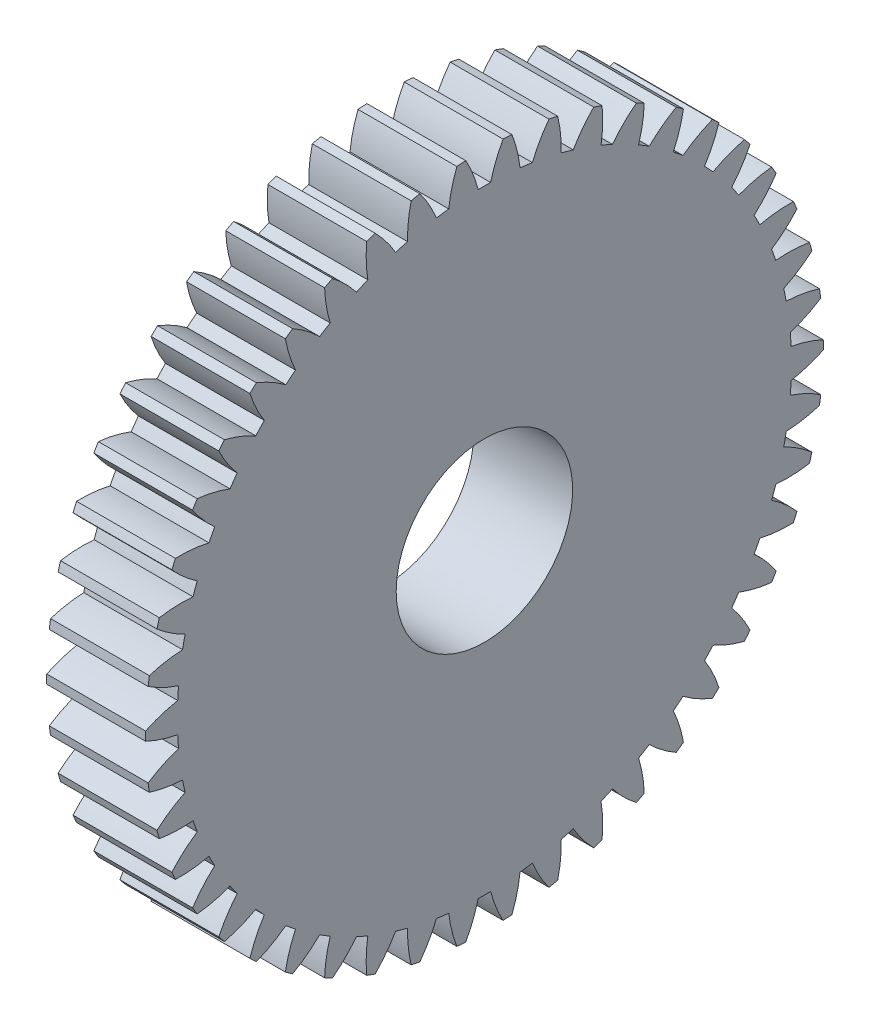
SolidWorks part; units mm, degrees
ref_plane "Plane1" through (0, 0, 0) normal (0, 0, 1) x (1, 0, 0)
ref_plane "Plane2" through (0, 0, 0) normal (0, 1, 0) x (1, 0, 0)
ref_plane "Plane3" through (0, 0, 0) normal (1, 0, 0) x (0, 0, -1)
sketch "HoldingSke" plane through (0, 0, 0) normal (0, 1, 0) x (1, 0, 0)
  line L0 (0, 0) -> (1.7366, -1.7983)
  line L1 (-15, 0) -> (100, 0) construction
  line L2 (0, 0) -> (-2.1039, 2.3779)
  line L3 (0, 0) -> (-11.863, 4.5341)
  line L4 (0, 0) -> (5.9991, 6.2122)
  line L5 (0, 0) -> (-46.8476, -17.4728)
  line L6 (0, 0) -> (-2.3211, -1.5661)
  line L7 (-2.1039, 2.3779) -> (8.6586, 51.2059)
  line L8 (-76.2, 54.61) -> (-75.3, 54.61)
  line L9 (-71.009, 38.7566) -> (-53.1078, 45.2721)
  line L10 (-76.2, 71.12) -> (104.1128, 71.12)
  line L11 (0, 0) -> (-2.8, 0)
  line L12 (-76.2, 101.6) -> (-76.185, 101.6)
  line L13 (24.9733, 27.94) -> (52.9518, 28.4284)
  line L14 (24.9733, 27.94) -> (24.9743, 27.94)
  line L15 (24.9733, 27.94) -> (100.4006, 29.5858)
  line L16 (-63.627, -0.4) -> (-12.827, -0.4)
  circle A0 centre (0, 0) radius 2.5
  circle A1 centre (0, 0) radius 8.699
  circle A2 centre (0, 0) radius 37.5
  circle A3 centre (0, 0) radius 2.5
  dimension "Hub_dia" = 75
  dimension "Overall_len" = 50
  dimension "OAL" = 50.0001
  dimension "Ap" = 20
  dimension "H" = 19.05
  dimension "Pitch_radius" = 180.3128
  dimension "Addendum_fac" = 1
  dimension "Dedendum_fac" = 1.25
  dimension "Clearance_fac" = 0.25
  dimension "Dedendum_add" = 0.001
sketch "BasProSke" plane through (0, 0, 0) normal (0, 1, 0) x (1, 0, 0)
  line L0 (-10, 0) -> (60, 0) construction
  line L1 (0, 0) -> (0, 9.6)
  line L2 (0, 0) -> (2.8, 0)
  line L3 (2.8, 0) -> (2.8, 9.6)
  line L4 (2.8, 9.6) -> (0, 9.6)
revolve "Base-Revolve" add sketch "BasProSke" angle 360 about L0
sketch "TooCutSke" plane through (0, 0, 0) normal (1, 0, 0) x (0, 0, -1)
  line L1 (0, 0) -> (0, 107) construction
  line L2 (0, 0) -> (-0.3403, 9.1937) construction
  line L3 (0, 0) -> (-1.255, 18.3481) construction
  line L4 (-0.3403, 9.1937) -> (-0.6275, 9.1741) construction
  arc A0 (0.1761, 8.6972) -> (-0.1761, 8.6972) centre (0, 0) ccw
  arc A1 (0.5433, 9.6101) -> (-0.5433, 9.6101) centre (0, 0) ccw
  circle A2 centre (0, 0) radius 9.2 construction
  circle A3 centre (0, 0) radius 8.6452 construction
  arc A4 (-0.1761, 8.6972) -> (-0.5433, 9.6101) centre (-3.7432, 7.7928) ccw
  arc A5 (0.5433, 9.6101) -> (0.1761, 8.6972) centre (3.7432, 7.7928) ccw
extrude "ToothCut" cut sketch "TooCutSke" along normal through all
fillet "Breaks" [suppressed] radius 0.008
fillet "RootFillets" [suppressed] radius 0.101
pattern_circular "TeethCuts" count 46 every 7.826 about axis through (-10, 0, 0) along (1, 0, 0) of "ToothCut", "RootFillets", "Breaks"
sketch "HubNeaOneSke" plane through (0, 0, 0) normal (-1, 0, 0) x (0, 0, 1)
  circle A0 centre (0, 0) radius 8.699
extrude "HubNearOne" [suppressed] add sketch "HubNeaOneSke" along normal blind 47.2001
sketch "HubNeaBotSke" plane through (0, 0, 0) normal (-1, 0, 0) x (0, 0, 1)
  circle A0 centre (0, 0) radius 8.699
extrude "HubNearBoth" [suppressed] add sketch "HubNeaBotSke" along normal blind 23.6
ref_plane "FarPln" through (2.8, 0, 0) normal (1, 0, 0) x (0, 0, -1)
sketch "HubFarSke" plane through (2.8, 0, 0) normal (1, 0, 0) x (0, 0, -1)
  circle A0 centre (0, 0) radius 8.699
extrude "HubFar" [suppressed] add sketch "HubFarSke" along normal blind 23.6
sketch "BorSke" plane through (0, 0, 0) normal (1, 0, 0) x (0, 0, -1)
  circle A0 centre (0, 0) radius 2.5
extrude "Bore" cut sketch "BorSke" along normal mid plane 100.0001
sketch "KeySke" plane through (0, 0, 0) normal (1, 0, 0) x (0, 0, -1)
  line L0 (-1, 0) -> (-1, 3.4)
  line L1 (-1, 3.4) -> (1, 3.4)
  line L2 (1, 3.4) -> (1, 0)
  line L3 (0, 0) -> (0, 34) construction
  line L4 (-1, 0) -> (1, 0)
extrude "Keyway" [suppressed] cut sketch "KeySke" along normal mid plane 100.0001
pattern_circular "Keyway2" [suppressed] count 2 every 90 about axis through (-10, 0, 0) along (1, 0, 0)
equation "' \"Module@HoldingSke\" = 6.35"
equation "' \"Num_teeth@HoldingSke\" = 12"
equation "' \"Ap@HoldingSke\" =  20"
equation "' \"Ap@HoldingSke\" = 20"
equation "' \"Width@HoldingSke\" = 0.5 * 25.4"
equation "' \"Hub_dia@HoldingSke\"= 1 * 25.4"
equation "' \"Hub_dia@HoldingSke\" = 1 * 25.4"
equation "' \"Overall_len@HoldingSke\" = 1.0 * 25.4"
equation "' \"Bore@HoldingSke\" = 0.75 * 25.4"
equation "' \"T_dim@HoldingSke\" = 0.1 * 25.4"
equation "' \"Width@KeySke\" = 0.25 * 25.4"
equation "' \"Show_teeth@HoldingSke\" = 13"
equation "' \"Backlash@HoldingSke\" = 0.009 * 25.4"
equation "' \"Addendum_fac@HoldingSke\" = 1.0"
equation "' \"Dedendum_fac@HoldingSke\" = 1.25"
equation "' \"Dedendum_add@HoldingSke\" = 0.00005 * 25.4"
equation "' \"Clearance_fac@HoldingSke\" = 0.25"
equation "\"Pitch@HoldingSke\" = 1 / \"Module@HoldingSke\""
equation "\"Overcut_dia@TooCutSke\" = (\"Num_teeth@HoldingSke\" + 2 * \"Addendum_fac@HoldingSke\") / \"Pitch@HoldingSke\" + 0.002 * 25.4"
equation "\"Pitch_dia@TooCutSke\" = \"Num_teeth@HoldingSke\" / \"Pitch@HoldingSke\""
equation "\"Base_dia@TooCutSke\" = \"Num_teeth@HoldingSke\" / \"Pitch@HoldingSke\" * cos((\"Ap@HoldingSke\"  * 3.14159265 / 180))"
equation "\"Root_dia@TooCutSke\" = (\"Num_teeth@HoldingSke\" + 2) / \"Pitch@HoldingSke\" - 2 * (\"Addendum_fac@HoldingSke\" + \"Dedendum_fac@HoldingSke\") / \"Pitch@HoldingSke\" - \"Dedendum_add@HoldingSke\" * 2"
equation "\"Half_ang@TooCutSke\" = 180 / \"Num_teeth@HoldingSke\""
equation "\"Half_CT@TooCutSke\" = \"Num_teeth@HoldingSke\" / \"Pitch@HoldingSke\" * sin((3.14159265 / 2 / \"Num_teeth@HoldingSke\")) / 2 - 7 * \"Backlash@HoldingSke\" / 4"
equation "\"Flank_rad@TooCutSke\" = \"Num_teeth@HoldingSke\" / \"Pitch@HoldingSke\" / 5"
equation "\"Radius@RootFillets\" = \"Clearance_fac@HoldingSke\" / \"Pitch@HoldingSke\" + \"Dedendum_add@HoldingSke\""
equation "\"Break_rad@Breaks\" = 0.02 / \"Pitch@HoldingSke\""
equation "\"Thickness@HoldingSke\" = \"Width@HoldingSke\""
equation "\"OAL@HoldingSke\" = \"Thickness@HoldingSke\""
equation "\"MHD@HoldingSke\" = (\"Num_teeth@HoldingSke\" + 2) / \"Pitch@HoldingSke\" - 2 * (\"Addendum_fac@HoldingSke\" + \"Dedendum_fac@HoldingSke\")  / \"Pitch@HoldingSke\" - \"Dedendum_add@HoldingSke\" * 2"
equation "\"MBD@HoldingSke\" = (\"Num_teeth@HoldingSke\" + 2) / \"Pitch@HoldingSke\" - 2 * (\"Addendum_fac@HoldingSke\" + \"Dedendum_fac@HoldingSke\")  / \"Pitch@HoldingSke\" - \"Dedendum_add@HoldingSke\" * 2 - 0.002 * 25.4"
equation "\"MHD@HoldingSke\" = ((sgn( \"MHD@HoldingSke\" - \"Hub_dia@HoldingSke\" )-1)*( \"MHD@HoldingSke\" - \"Hub_dia@HoldingSke\" ))/-2+ \"Hub_dia@HoldingSke\""
equation "\"MBD@HoldingSke\" = ((sgn( \"MBD@HoldingSke\" - \"Bore@HoldingSke\" )-1)*( \"MBD@HoldingSke\" - \"Bore@HoldingSke\" ))/-2+ \"Bore@HoldingSke\""
equation "\"OAL@HoldingSke\" = ((sgn( \"OAL@HoldingSke\" - \"Overall_len@HoldingSke\" )+1)*( \"OAL@HoldingSke\" - \"Overall_len@HoldingSke\" ))/2 + \"Overall_len@HoldingSke\" + 0.000002 * 25.4"
equation "\"Num_teeth@TeethCuts\" = int( \"Show_teeth@HoldingSke\" ) + 1"
equation "\"Num_teeth@TeethCuts\" = ((sgn( \"Num_teeth@TeethCuts\" - \"Num_teeth@HoldingSke\" )-1)*( \"Num_teeth@TeethCuts\" - \"Num_teeth@HoldingSke\" ))/-2+ \"Num_teeth@HoldingSke\""
equation "\"Num_teeth@TeethCuts\" = ((sgn( \"Num_teeth@TeethCuts\" - 2.0)+1)*( \"Num_teeth@TeethCuts\" - 2.0))/2 +2.0"
equation "\"Angle@TeethCuts\" = 360.0 / \"Num_teeth@HoldingSke\""
equation "\"Diameter@BasProSke\" = (\"Num_teeth@HoldingSke\" + 2 * \"Addendum_fac@HoldingSke\") / \"Pitch@HoldingSke\""
equation "\"Thickness@BasProSke\"  = \"Thickness@HoldingSke\""
equation "' \"Fillet_rad@BasProSke\" =  \"Thickness@HoldingSke\" * 0.05"
equation "' \"Fillet_rad@BasProSke\" = \"Thickness@HoldingSke\" * 0.05"
equation "\"MHD@HoldingSke\" = ((sgn( \"MHD@HoldingSke\" - \"Root_dia@TooCutSke\" )-1)*( \"MHD@HoldingSke\" - \"Root_dia@TooCutSke\" ))/-2+ \"Root_dia@TooCutSke\""
equation "\"Diameter@HubNeaOneSke\" = \"MHD@HoldingSke\""
equation "\"Length@HubNearOne\" = \"OAL@HoldingSke\" - \"Thickness@BasProSke\""
equation "\"Diameter@HubNeaBotSke\" = \"MHD@HoldingSke\""
equation "\"Length@HubNearBoth\" = ( \"OAL@HoldingSke\" - \"Thickness@BasProSke\" ) / 2.0"
equation "\"Thickness@FarPln\" = \"Thickness@BasProSke\""
equation "\"Diameter@HubFarSke\" = \"MHD@HoldingSke\""
equation "\"Length@HubFar\" = ( \"OAL@HoldingSke\" - \"Thickness@BasProSke\" ) / 2.0"
equation "\"Diameter@BorSke\" = \"MBD@HoldingSke\""
equation "\"D1@Bore\" = \"OAL@HoldingSke\" * 2.0"
equation "\"D1@Keyway\" = \"OAL@HoldingSke\" * 2.0"
equation "\"Offset@KeySke\" = \"T_dim@HoldingSke\" + \"MBD@HoldingSke\" / 2.0"
